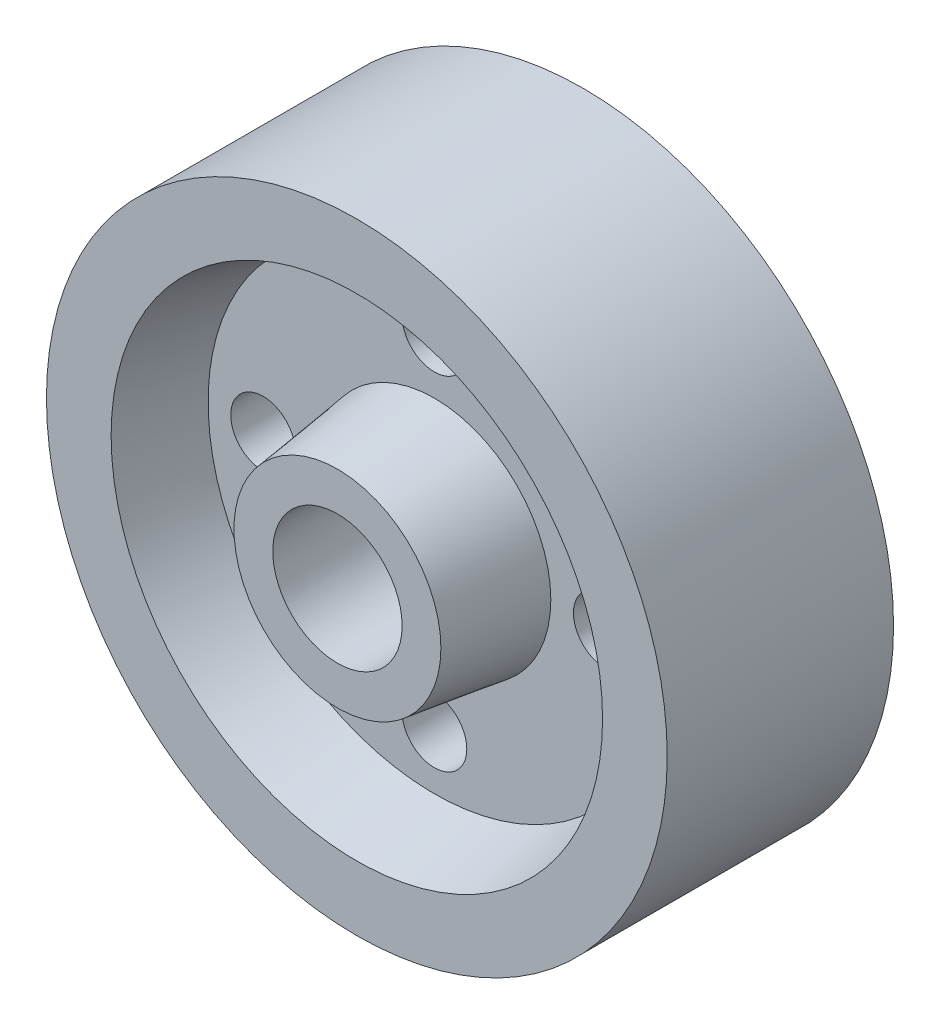
SolidWorks part; units mm, degrees
ref_plane "Front Plane" through (0, 0, 0) normal (0, 0, 1) x (1, 0, 0)
ref_plane "Top Plane" through (0, 0, 0) normal (0, 1, 0) x (1, 0, 0)
ref_plane "Right Plane" through (0, 0, 0) normal (1, 0, 0) x (0, 0, -1)
sketch "Sketch1" plane through (0, 0, 0) normal (1, 0, 0) x (0, 0, -1)
  line L0 (0, 0) -> (0, 10) construction
  line L1 (-20.5, 0) -> (20.5, 0) construction
  line L2 (-20.5, 10) -> (20.5, 10)
  line L3 (-20.5, 10) -> (-20.5, 16)
  line L4 (-5.5, 10) -> (5.5, 10)
  line L5 (-5.5, 10) -> (-5.5, 35)
  line L6 (-5.5, 35) -> (5.5, 35)
  line L7 (5.5, 10) -> (5.5, 35)
  line L8 (-20.5, 16) -> (-5.5, 18)
  line L9 (-5.5, 35) -> (-17.5, 38)
  line L10 (-17.5, 48) -> (-17.5, 38)
  line L11 (5.5, 35) -> (17.5, 38)
  line L12 (17.5, 48) -> (17.5, 38)
  line L13 (20.5, 10) -> (20.5, 16)
  line L14 (20.5, 16) -> (5.5, 18)
  line L15 (-17.5, 48) -> (17.5, 48)
  point P6 (0, 0)
  point P8 (0, 10)
  dimension "D1" = 41
  dimension "D2" = 11
  dimension "D3" = 20
  dimension "D4" = 70
  dimension "D5" = 18
  dimension "D6" = 16
  dimension "D7" = 35
  dimension "D8" = 10
  dimension "D9" = 76
revolve "Revolve1" add sketch "Sketch1" angle 360 about L1
sketch "Sketch2" plane through (0, 0, -5.5) normal (0, 0, -1) x (-1, 0, 0)
  circle A0 centre (0, 0) radius 26.5 construction
  circle A1 centre (0, 26.5) radius 5
  circle A2 centre (26.5, 0) radius 5
  circle A3 centre (0, -26.5) radius 5
  circle A4 centre (-26.5, 0) radius 5
  point P5 (-26.5, 0)
  dimension "D1" = 53
  dimension "D2" = 10
  dimension "D3" = 4
extrude "Cut-Extrude1" cut sketch "Sketch2" against normal through all
